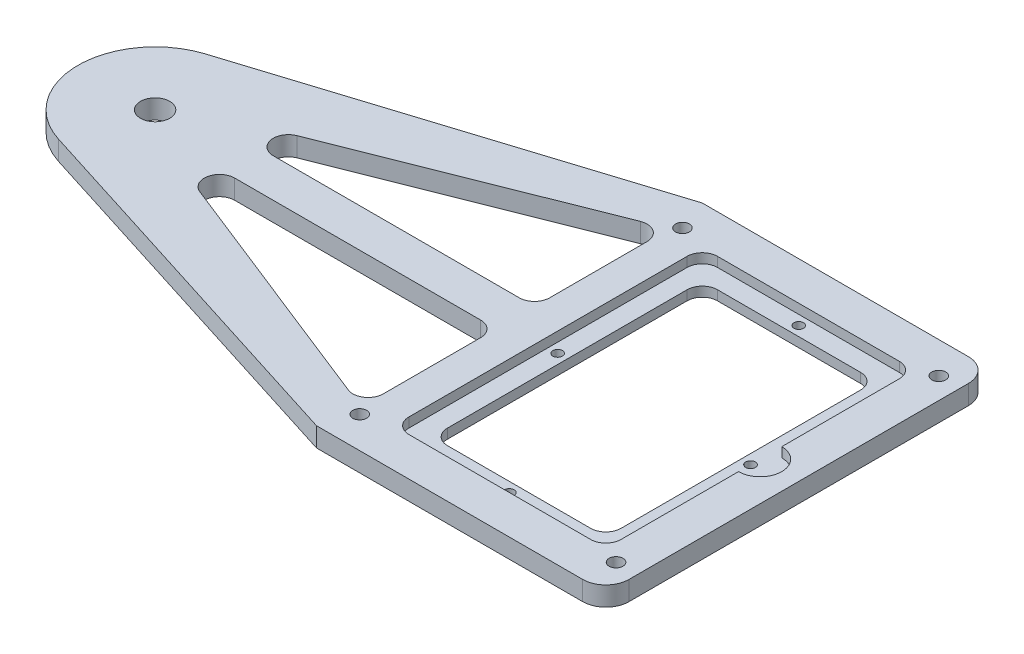
SolidWorks part; units mm, degrees
material "UHMW"
ref_plane "Front Plane" through (0, 0, 0) normal (0, 0, 1) x (1, 0, 0)
ref_plane "Top Plane" through (0, 0, 0) normal (0, 1, 0) x (1, 0, 0)
ref_plane "Right Plane" through (0, 0, 0) normal (1, 0, 0) x (0, 0, -1)
sketch "Sketch1" plane through (0, 0, 0) normal (0, 1, 0) x (1, 0, 0)
  line L0 (-47.625, 0) -> (47.625, 0) construction
  line L1 (-47.625, -63.5) -> (47.625, -63.5)
  line L2 (-47.625, -63.5) -> (-47.625, 63.5)
  line L3 (-47.625, 63.5) -> (47.625, 63.5)
  line L4 (47.625, -63.5) -> (47.625, 63.5)
  line L5 (-47.625, -63.5) -> (47.625, 63.5) construction
  line L6 (-47.625, 63.5) -> (47.625, -63.5) construction
  point P0 (0, 0)
  dimension "D1" = 95.25
  dimension "D2" = 127
  dimension "D3" = 63.5
extrude "Boss-Extrude1" add sketch "Sketch1" along normal blind 6.35
sketch "Sketch4" plane through (0, 6.35, 0) normal (0, 1, 0) x (1, 0, 0)
  line L1 (-47.625, 63.5) -> (-171.916, 24.2193)
  line L5 (-47.625, 63.5) -> (-47.625, -63.5) construction
  line L9 (-47.625, -63.5) -> (-171.916, -24.2193)
  line L10 (-47.625, 63.5) -> (-47.625, -63.5)
  arc A0 (-171.916, 24.2193) -> (-171.916, -24.2193) centre (-164.2618, 0) ccw
  circle A1 centre (-48.9458, 0) radius 2.5 construction
  dimension "D1" = 50.8
  dimension "D2" = 115.316
extrude "Boss-Extrude3" add sketch "Sketch4" against normal blind 6.35
sketch "Sketch5" plane through (0, 6.35, 0) normal (0, 1, 0) x (1, 0, 0)
  circle A0 centre (-164.2618, 0) radius 4.826
  circle A1 centre (-8.6868, 0) radius 4.826
  arc A2 (-171.916, 24.2193) -> (-171.916, -24.2193) centre (-164.2618, 0) ccw construction
  arc A3 (-171.916, 24.2193) -> (-171.916, -24.2193) centre (-164.2618, 0) ccw
  dimension "D1" = 9.652
  dimension "D2" = 155.575
extrude "Cut-Extrude1" cut sketch "Sketch5" against normal through all contours A0 | A1
sketch "Sketch6" plane through (0, 6.35, 0) normal (0, 1, 0) x (1, 0, 0)
  line L0 (-45.72, 6.35) -> (-45.72, -6.35) construction
  line L1 (-45.72, 50.7829) -> (-157.9118, 6.35)
  line L2 (-157.9118, 6.35) -> (-45.72, 6.35)
  line L3 (-45.72, 6.35) -> (-45.72, 50.7829)
  line L4 (-45.72, -6.35) -> (-45.72, -50.7829)
  line L5 (-45.72, -50.7829) -> (-157.9118, -6.35)
  line L6 (-157.9118, -6.35) -> (-45.72, -6.35)
  line L7 (0, 0) -> (-45.72, 0) construction
  line L8 (-47.625, 63.5) -> (-171.916, 24.2193) construction
  line L9 (-189.6618, 78.2466) -> (-189.6618, -78.2466) construction
  arc A1 (-171.916, 24.2193) -> (-171.916, -24.2193) centre (-164.2618, 0) ccw construction
  point P10 (-189.6618, 0)
  dimension "D1" = 12.7
  dimension "D2" = 31.75
  dimension "D3" = 12.7
  dimension "D4" = 45.72
extrude "Cut-Extrude2" cut sketch "Sketch6" against normal through all
fillet "Fillet9" radius 5 6 edges at (-157.9118, 3.175, 6.35) (-45.72, 3.175, 6.35) (-45.72, 3.175, 50.7829) (-45.72, 3.175, -6.35) (-157.9118, 3.175, -6.35) (-45.72, 3.175, -50.7829)
sketch "Sketch7" plane through (0, 6.35, 0) normal (0, 1, 0) x (1, 0, 0)
  circle A0 centre (-8.6868, 0) radius 5.4538
extrude "Boss-Extrude4" add sketch "Sketch7" against normal blind 6.35
sketch "Sketch8" plane through (0, 6.35, 0) normal (0, 1, 0) x (1, 0, 0)
  line L4 (-47.625, -63.5) -> (47.625, -63.5) construction
  line L5 (-34.925, 50.8) -> (-34.925, -50.8)
  line L7 (-47.625, 63.5) -> (-47.625, -63.5) construction
  line L8 (-171.916, -24.2193) -> (-47.625, -63.5) construction
  line L10 (47.625, 50.8) -> (-47.625, 50.8)
  line L11 (34.925, 50.8) -> (-34.925, 50.8)
  line L13 (34.925, -63.5) -> (34.925, 63.5)
  line L14 (34.925, -50.8) -> (34.925, 50.8)
  line L15 (-34.925, 63.5) -> (-34.925, -63.5) construction
  line L16 (-47.625, -50.8) -> (47.625, -50.8)
  line L17 (-34.925, -50.8) -> (34.925, -50.8)
  dimension "D1" = 12.7
  dimension "D2" = 12.7
  dimension "D3" = 12.7
  dimension "D4" = 12.7
extrude "Cut-Extrude3" cut sketch "Sketch8" against normal blind 3.175
sketch "Sketch9" plane through (0, 3.175, 0) normal (0, 1, 0) x (1, 0, 0)
  line L14 (-28.575, -44.45) -> (28.575, -44.45)
  line L15 (28.575, -44.45) -> (28.575, 44.45)
  line L16 (-28.575, 44.45) -> (-28.575, -44.45)
  line L17 (28.575, 44.45) -> (-28.575, 44.45)
  line L18 (-28.575, -44.45) -> (28.575, -44.45)
  line L19 (28.575, -44.45) -> (28.575, 44.45)
  line L20 (-28.575, 44.45) -> (-28.575, -44.45)
  line L21 (28.575, 44.45) -> (-28.575, 44.45)
  dimension "D1" = 6.35
extrude "Cut-Extrude4" cut sketch "Sketch9" against normal through all
sketch "Sketch11" plane through (0, 3.175, 0) normal (0, 1, 0) x (1, 0, 0)
  line L0 (0, 50.8) -> (0, -50.8) construction
  line L1 (34.925, 50.8) -> (-34.925, 50.8) construction
  line L2 (-34.925, -50.8) -> (34.925, -50.8) construction
  line L3 (-34.925, 0) -> (34.925, 0) construction
  line L4 (-34.925, 50.8) -> (-34.925, -50.8) construction
  line L5 (34.925, -50.8) -> (34.925, 50.8) construction
  line L6 (-34.925, 50.8) -> (-34.925, -50.8) construction
  line L7 (-28.575, 44.45) -> (-28.575, -44.45) construction
  line L8 (34.925, 50.8) -> (-34.925, 50.8) construction
  circle A0 centre (-31.75, 0) radius 1.5875
  circle A1 centre (31.75, 0) radius 1.5875
  circle A2 centre (0, 47.625) radius 1.5875
  circle A3 centre (0, -47.625) radius 1.5875
  dimension "D1" = 3.175
  dimension "D4" = 3.175
  dimension "D2" = 3.175
  dimension "D3" = 3.175
  dimension "D5" = 3.175
extrude "Cut-Extrude6" cut sketch "Sketch11" against normal through all
sketch "Sketch12" plane through (0, 6.35, 0) normal (0, 1, 0) x (1, 0, 0)
  line L0 (34.925, -50.8) -> (34.925, 50.8) construction
  line L1 (34.925, 7.112) -> (34.925, 50.8) construction
  line L2 (34.925, -7.112) -> (34.925, -50.8) construction
  line L3 (34.925, 0) -> (-34.925, 0) construction
  line L4 (-34.925, 50.8) -> (-34.925, -50.8) construction
  line L5 (34.925, -50.8) -> (34.925, 50.8) construction
  line L6 (34.925, 7.112) -> (34.925, -7.112)
  arc A0 (34.925, 7.112) -> (34.925, -7.112) centre (34.925, 0) cw
  dimension "D1" = 7.112
extrude "Cut-Extrude7" cut sketch "Sketch12" against normal blind 3.175
fillet "Fillet10" radius 5 4 edges at (-34.925, 4.7625, 50.8) (34.925, 4.7625, 50.8) (34.925, 4.7625, -50.8) (-34.925, 4.7625, -50.8)
fillet "Fillet11" radius 5 4 edges at (-28.575, 1.5875, -44.45) (28.575, 1.5875, -44.45) (28.575, 1.5875, 44.45) (-28.575, 1.5875, 44.45)
fillet "Fillet12" radius 7.62 2 edges at (47.625, 3.175, -63.5) (47.625, 3.175, 63.5)
sketch "Sketch13" plane through (0, 6.35, 0) normal (0, 1, 0) x (1, 0, 0)
  circle A0 centre (-43.7773, 53.1254) radius 2.2812
  circle A1 centre (-43.7773, -53.1254) radius 2.2812
  circle A2 centre (40.6023, -53.1254) radius 2.2812
  circle A3 centre (40.6023, 53.1254) radius 2.2812
  circle A8 centre (-43.7773, 53.1254) radius 2.2812 construction
  circle A9 centre (40.6023, 53.1254) radius 2.2812 construction
  circle A10 centre (40.6023, -53.1254) radius 2.2812 construction
  circle A11 centre (-43.7773, -53.1254) radius 2.2812 construction
extrude "Cut-Extrude8" cut sketch "Sketch13" against normal through all
